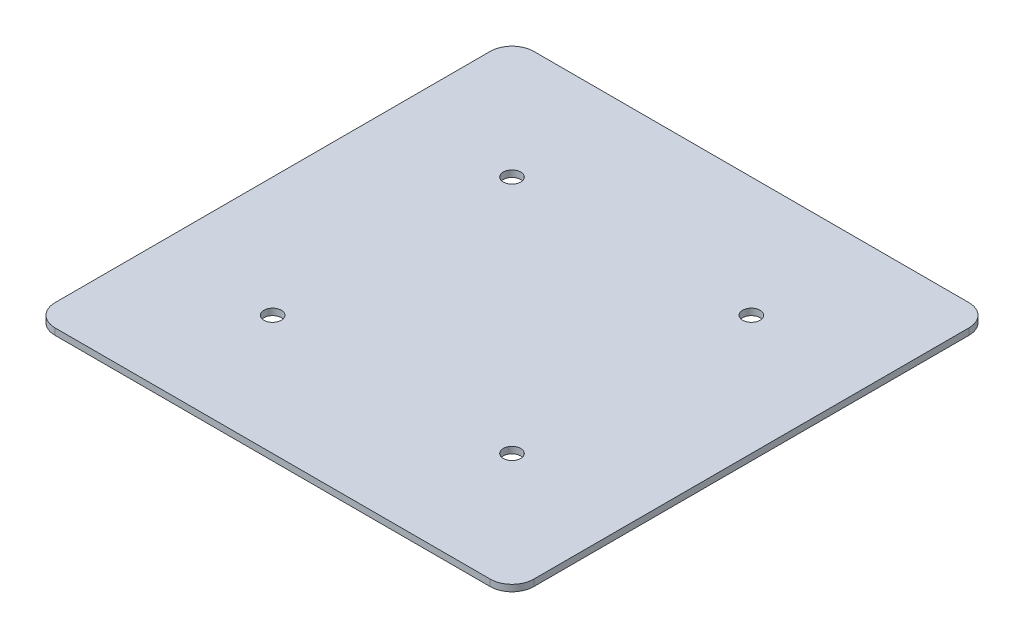
SolidWorks part; units mm, degrees
ref_plane "前视基准面" through (0, 0, 0) normal (0, 0, 1) x (1, 0, 0)
ref_plane "上视基准面" through (0, 0, 0) normal (0, 1, 0) x (1, 0, 0)
ref_plane "右视基准面" through (0, 0, 0) normal (1, 0, 0) x (0, 0, -1)
other "Configuration Table"
sketch "草图1" plane through (0, 0, 0) normal (0, 1, 0) x (1, 0, 0)
  line L1 (0, 0) -> (88, 0)
  line L2 (0, 0) -> (0, -88)
  line L3 (0, -88) -> (88, -88)
  line L4 (88, 0) -> (88, -88)
  dimension "D1" = 88
extrude "凸台-拉伸1" add sketch "草图1" along normal blind 1.2
fillet "圆角1" radius 4 4 edges at (0, 0.6, 0) (88, 0.6, 0) (88, 0.6, 88) (0, 0.6, 88)
sketch "草图2" plane through (0, 1.2, 0) normal (0, 1, 0) x (1, 0, 0)
  circle A0 centre (22, -22) radius 1.6
  circle A1 centre (66, -22) radius 1.6
  circle A2 centre (66, -66) radius 1.6
  circle A3 centre (22, -66) radius 1.6
  dimension "D1" = 3.2
extrude "切除-拉伸1" cut sketch "草图2" along direction (0, 1, 0) on the side of the normal blind 10 and the other way through all
